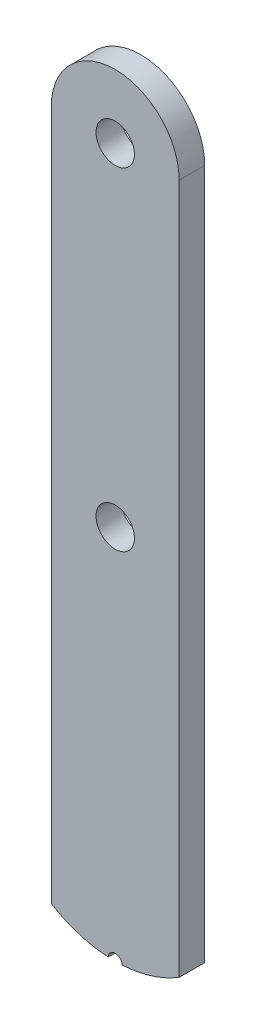
SolidWorks part; units mm, degrees
ref_plane "Front Plane" through (0, 0, 0) normal (0, 0, 1) x (1, 0, 0)
ref_plane "Top Plane" through (0, 0, 0) normal (0, 1, 0) x (1, 0, 0)
ref_plane "Right Plane" through (0, 0, 0) normal (1, 0, 0) x (0, 0, -1)
sketch "Sketch1" plane through (0, 0, 0) normal (0, 0, 1) x (1, 0, 0)
  line L0 (0, 24.5) -> (0, -30.5) construction
  line L2 (-5, 24.5) -> (-5, -29.5)
  line L4 (5, 24.5) -> (5, -29.5)
  line L5 (-5, 29.5) -> (5, -29.5) construction
  line L6 (-5, -29.5) -> (5, 29.5) construction
  circle A0 centre (0, 24.5) radius 1.5
  arc A1 (5, 24.5) -> (-5, 24.5) centre (0, 24.5) ccw
  circle A2 centre (0, -1.5) radius 1.5
  arc A3 (5, -29.5) -> (-5, -29.5) centre (0, -21.3648) cw
  point P0 (0, 0)
  dimension "D3" = 3
  dimension "D4" = 26
  dimension "D1" = 59
  dimension "D2" = 10
extrude "Boss-Extrude1" add sketch "Sketch1" along normal blind 2
sketch "Sketch2" plane through (0, 0, 2) normal (0, 0, 1) x (1, 0, 0)
  circle A0 centre (0, -30.9137) radius 0.5504
  arc A1 (-5, -29.5) -> (5, -29.5) centre (0, -21.3648) ccw construction
extrude "Cut-Extrude1" cut sketch "Sketch2" against normal blind 10
